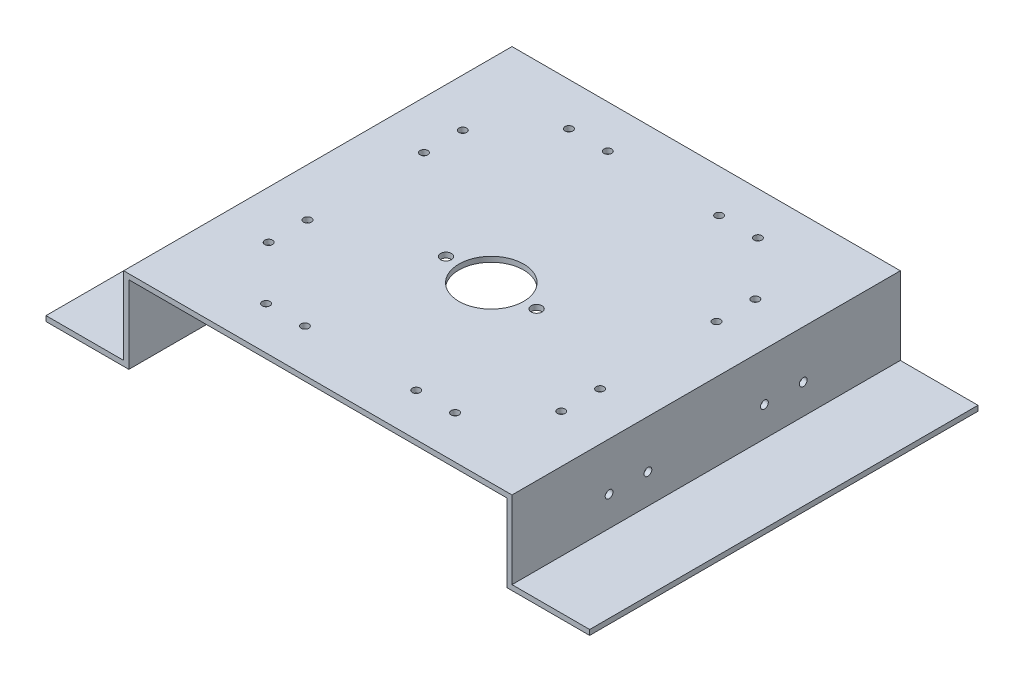
SolidWorks part; units mm, degrees
ref_plane "Front Plane" through (0, 0, 0) normal (0, 0, 1) x (1, 0, 0)
ref_plane "Top Plane" through (0, 0, 0) normal (0, 1, 0) x (1, 0, 0)
ref_plane "Right Plane" through (0, 0, 0) normal (1, 0, 0) x (0, 0, -1)
sketch "Sketch1" plane through (0, 0, 0) normal (0, 0, 1) x (1, 0, 0)
  line L0 (-75, 16) -> (75, 16)
  line L1 (75, 16) -> (75, -14)
  line L2 (75, -14) -> (105, -14)
  line L3 (105, -14) -> (105, -16)
  line L4 (105, -16) -> (73, -16)
  line L5 (73, -16) -> (73, 14)
  line L6 (73, 14) -> (-73, 14)
  line L7 (-73, 14) -> (-73, -16)
  line L8 (-73, -16) -> (-105, -16)
  line L9 (-105, -16) -> (-105, -14)
  line L10 (-105, -14) -> (-75, -14)
  line L11 (-75, -14) -> (-75, 16)
  line L12 (0, 65.0171) -> (0, -52.7304) construction
  line L13 (-104.5375, 0) -> (123.7396, 0) construction
  dimension "D1" = 150
  dimension "D2" = 2
  dimension "D3" = 2
  dimension "D4" = 2
  dimension "D5" = 2
  dimension "D6" = 2
  dimension "D7" = 30
  dimension "D8" = 30
  dimension "D9" = 30
  dimension "D10" = 30
  dimension "D11" = 16
  dimension "D12" = 75
extrude "Boss-Extrude1" add sketch "Sketch1" against normal blind 150
sketch "Sketch2" plane through (0, 16, 0) normal (0, 1, 0) x (1, 0, 0)
  line L0 (-50, 75) -> (17.3451, 75) construction
  line L1 (75, 0) -> (-75, 0) construction
  line L2 (0, 35.969) -> (0, 152.9677) construction
  circle A1 centre (0, 67) radius 12.5
  point P2 (0, 67)
  dimension "D2" = 25
  dimension "D1" = 8
  dimension "D3" = 75
extrude "Cut-Extrude1" cut sketch "Sketch2" against normal up to next
sketch "Sketch3" plane through (0, 16, 0) normal (0, 1, 0) x (1, 0, 0)
  line L0 (0, 126.6339) -> (0, -31.1551) construction
  line L1 (-112.1251, 75) -> (129.3056, 75) construction
  line L2 (-112.1251, 67) -> (129.3056, 67) construction
  circle A1 centre (17.5, 67) radius 2.1
  circle A2 centre (-17.5, 67) radius 2.1
  point P7 (17.5, 67)
  dimension "D4" = 4.2
  dimension "D1" = 75
  dimension "D2" = 8
  dimension "D3" = 17.5
extrude "Cut-Extrude2" cut sketch "Sketch3" against normal up to next
sketch "Sketch4" plane through (0, 14, 0) normal (0, -1, 0) x (1, 0, 0)
  line L0 (-136.5409, -16.5) -> (155.158, -16.5) construction
  line L1 (56.5, 28.3064) -> (56.5, -199.6034) construction
  line L2 (0, 45.039) -> (0, -185.1787) construction
  line L3 (-136.5409, -75) -> (155.158, -75) construction
  line L4 (-73, 0) -> (73, 0) construction
  line L5 (73, -150) -> (73, 0) construction
  line L6 (-136.5409, -133.5) -> (155.158, -133.5) construction
  line L7 (-56.5, 28.3064) -> (-56.5, -199.6034) construction
  line L10 (-29, 29.8064) -> (-29, -188.3398) construction
  line L11 (-136.5409, -105) -> (159.6044, -105) construction
  line L12 (29, 29.8064) -> (29, -188.3398) construction
  line L13 (-136.5409, -45) -> (159.6044, -45) construction
  point P25 (-36.5, -133.5)
  point P26 (-21.5, -133.5)
  point P27 (-56.5, -97.5)
  point P29 (-56.5, -112.5)
  point P31 (-56.5, -37.5)
  point P32 (-56.5, -52.5)
  point P34 (56.5, -37.5)
  point P35 (56.5, -52.5)
  point P36 (56.5, -97.5)
  point P37 (56.5, -112.5)
  point P39 (21.5, -133.5)
  point P40 (36.5, -133.5)
  point P41 (36.5, -16.5)
  point P42 (21.5, -16.5)
  point P43 (-21.5, -16.5)
  point P44 (-36.5, -16.5)
  dimension "D1" = 75
  dimension "D2" = 16.5
  dimension "D3" = 16.5
  dimension "D4" = 29
  dimension "D5" = 30
  dimension "D6" = 15
  dimension "D7" = 15
hole_wizard "Ø3.0mm Dowel Hole1" positions "Sketch7" profile "Sketch8" hole size "Ø3.0" standard "ANSI Metric" end condition up to next
sketch "Sketch7" plane through (0, 14, 0) normal (0, -1, 0) x (-1, 0, 0)
  point P0 (56.5, 97.5)
  point P3 (56.5, 112.5)
  point P6 (56.5, 52.5)
  point P9 (56.5, 37.5)
  point P12 (36.5, 16.5)
  point P15 (21.5, 16.5)
  point P18 (-21.5, 16.5)
  point P21 (-36.5, 16.5)
  point P24 (-56.5, 37.5)
  point P27 (-56.5, 52.5)
  point P30 (-56.5, 97.5)
  point P33 (-56.5, 112.5)
  point P36 (-36.5, 133.5)
  point P39 (-21.5, 133.5)
  point P42 (36.5, 133.5)
  point P45 (21.5, 133.5)
sketch "Sketch8" plane through (-56.5, 14, -97.5) normal (1, 0, 0) x (0, 0, -1)
  line L0 (0, 0) -> (0, 2)
  line L1 (0, 2) -> (1.5, 2)
  line L2 (1.5, 2) -> (1.5, 0)
  line L5 (1.5, 0) -> (0, 0)
  line L11 (0, -6.35) -> (0, 107.95) construction
  dimension "Thru Hole Dia." = 3
  dimension "Thru Hole Depth" = 2
sketch "Sketch15" plane through (73, 0, 0) normal (-1, 0, 0) x (0, 0, 1)
  line L0 (-155.8804, 0) -> (22.0565, 0) construction
  line L1 (-160.2921, -2.5) -> (18.135, -2.5) construction
  line L2 (-150, 14) -> (0, 14) construction
  line L3 (-75, 33.0782) -> (-75, -31.2819) construction
  line L4 (-150, 14) -> (-150, -16) construction
  line L5 (-45, 33.0782) -> (-45, -36.152) construction
  line L6 (-105, 33.0782) -> (-105, -36.152) construction
  point P13 (-52.5, -2.5)
  point P16 (-37.5, -2.5)
  point P23 (-112.5, -2.5)
  point P24 (-97.5, -2.5)
  dimension "D1" = 16.5
  dimension "D2" = 75
  dimension "D3" = 15
hole_wizard "Ø3.0mm Dowel Hole2" positions "Sketch16" profile "Sketch17" hole size "Ø3.0" standard "ANSI Metric" end condition up to next
sketch "Sketch16" plane through (73, 0, 0) normal (-1, 0, 0) x (0, 0, 1)
  point P0 (-112.5, -2.5)
  point P3 (-97.5, -2.5)
  point P6 (-52.5, -2.5)
  point P9 (-37.5, -2.5)
sketch "Sketch17" plane through (73, -2.5, -112.5) normal (0, 1, 0) x (0, 0, 1)
  line L0 (0, 0) -> (0, 2.001)
  line L1 (0, 2.001) -> (1.5, 2.001)
  line L2 (1.5, 2.001) -> (1.5, 0)
  line L5 (1.5, 0) -> (0, 0)
  line L11 (0, -6.35) -> (0, 107.95) construction
  dimension "Thru Hole Dia." = 3
  dimension "Thru Hole Depth" = 2.001
mirror "Mirror1" about plane through (0, 0, 0) normal (1, 0, 0) of "Ø3.0mm Dowel Hole2"
equation "\"TopLen\"= 150"
equation "\"D1@Sketch1\"=\"TopLen\""
equation "\"Thick\"=2"
equation "\"D2@Sketch1\"=\"Thick\""
equation "\"D3@Sketch1\"=\"Thick\""
equation "\"D4@Sketch1\"=\"Thick\""
equation "\"D5@Sketch1\"=\"Thick\""
equation "\"D6@Sketch1\"=\"Thick\""
equation "\"BottomLen\"= 30"
equation "\"D7@Sketch1\"=\"BottomLen\""
equation "\"D8@Sketch1\"=\"BottomLen\""
equation "\"Height\"= 30"
equation "\"D9@Sketch1\"=\"Height\""
equation "\"D10@Sketch1\"=\"Height\""
equation "\"D11@Sketch1\"=(\"Height\"+\"Thick\")/2"
equation "\"D12@Sketch1\"=\"TopLen\"/2"
equation "\"D1@Boss-Extrude1\"=\"TopLen\""
equation "\"D1@Sketch3\"=\"TopLen\"/2"
equation "\"D3@Sketch2\"=\"TopLen\"/2"
equation "\"D1@Sketch4\"=\"TopLen\"/2"
equation "\"Hole-Wall_Dist\"= 16.5"
equation "\"D2@Sketch4\"=\"Hole-Wall_Dist\""
equation "\"D3@Sketch4\"=\"Hole-Wall_Dist\""
equation "\"D4@Sketch4\"=(\"TopLen\"-4-30)/4"
equation "\"D5@Sketch4\"=(\"TopLen\"-30)/4"
equation "\"Hole-Hole_Dist\"=15"
equation "\"D6@Sketch4\"=\"Hole-Hole_Dist\""
equation "\"D7@Sketch4\"=\"Hole-Hole_Dist\""
equation "\"D1@Sketch15\"=\"Hole-Wall_Dist\""
equation "\"D2@Sketch15\"=\"TopLen\"/2"
equation "\"D3@Sketch15\"=\"Hole-Hole_Dist\""
